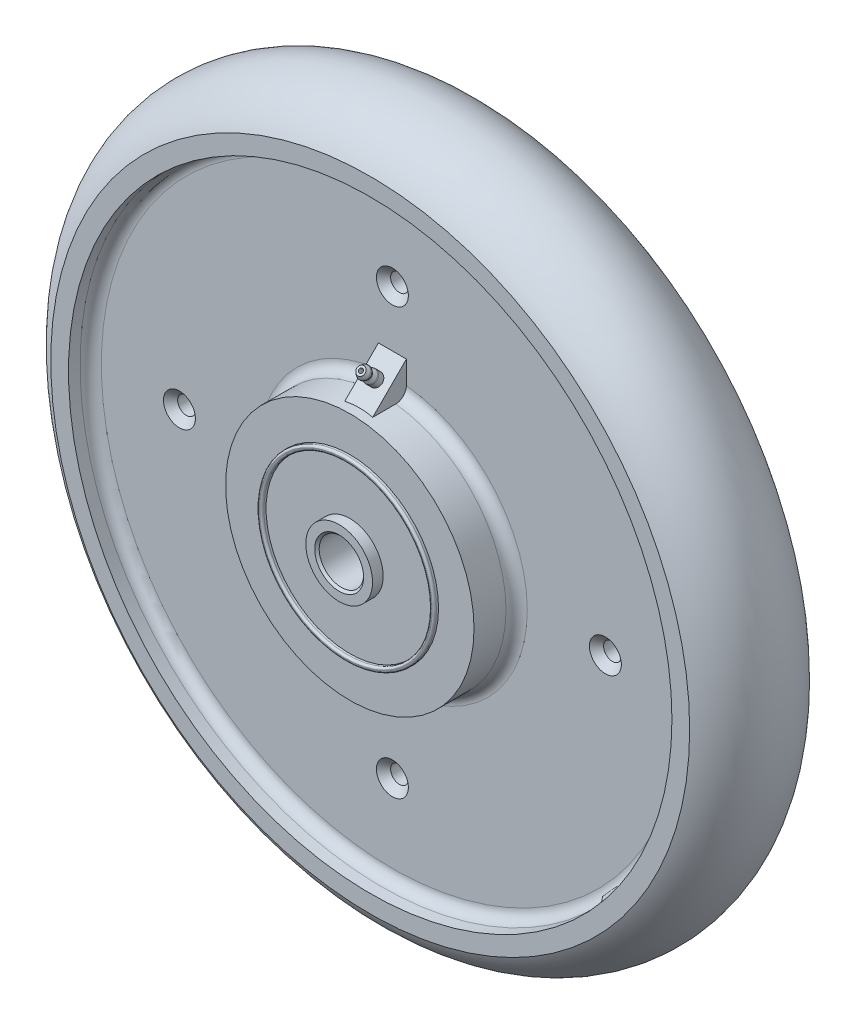
SolidWorks part; units mm, degrees
material "6061-T6 (SS)"
ref_plane "Front Plane" through (0, 0, 0) normal (0, 0, 1) x (1, 0, 0)
ref_plane "Top Plane" through (0, 0, 0) normal (0, 1, 0) x (1, 0, 0)
ref_plane "Right Plane" through (0, 0, 0) normal (1, 0, 0) x (0, 0, -1)
sketch "Sketch1" plane through (0, 0, 0) normal (1, 0, 0) x (0, 0, -1)
  line L0 (-31.75, 0) -> (31.75, 0) construction
  line L1 (31.75, -7.9375) -> (31.75, 7.9375) construction
  line L2 (0, -127) -> (0, 127) construction
  line L3 (-20.6375, 127) -> (20.6375, 127) construction
  line L4 (-20.6375, 127) -> (-20.6375, -127) construction
  line L5 (-20.6375, -127) -> (20.6375, -127) construction
  line L6 (20.6375, 127) -> (20.6375, -127) construction
  point P9 (-20.6375, 0)
  point P10 (0, 127)
  dimension "Hub Length" = 63.5
  dimension "For Axle Diameter" = 15.875
  dimension "Wheel Diameter" = 254
  dimension "Wheel Width" = 41.275
sketch "Sketch2" plane through (0, 0, 0) normal (1, 0, 0) x (0, 0, -1)
  line L0 (-31.75, 0) -> (31.75, 0) construction
  line L1 (-29.464, 31.75) -> (29.464, 31.75)
  line L2 (-29.464, 31.75) -> (-29.464, -31.75)
  line L3 (-29.464, -31.75) -> (29.464, -31.75)
  line L4 (29.464, 31.75) -> (29.464, -31.75)
  line L5 (-31.75, 11.9375) -> (31.75, 11.9375)
  line L6 (-31.75, 11.9375) -> (-31.75, -11.9375)
  line L7 (-31.75, -11.9375) -> (31.75, -11.9375)
  line L8 (31.75, 11.9375) -> (31.75, -11.9375)
  line L10 (-12.7, 107.95) -> (12.7, 107.95)
  line L11 (-12.7, 107.95) -> (-12.7, -107.95)
  line L12 (-12.7, -107.95) -> (12.7, -107.95)
  line L13 (12.7, 107.95) -> (12.7, -107.95)
  line L14 (-27.94, 44.45) -> (27.94, 44.45)
  line L15 (-27.94, 44.45) -> (-27.94, -44.45)
  line L16 (-27.94, -44.45) -> (27.94, -44.45)
  line L17 (27.94, 44.45) -> (27.94, -44.45)
  point P8 (-29.464, 0)
  point P11 (0, 31.75)
  point P19 (0, 107.95)
  point P20 (-12.7, 0)
  point P25 (-27.94, 0)
  point P26 (0, 44.45)
  dimension "Outer Hub Diameter" = 63.5
  dimension "Hub Diameter" = 23.875
  dimension "Outer Hub Length" = 58.928
  dimension "Inner Wheel Width" = 25.4
  dimension "Inner Wheel Diameter" = 215.9
  dimension "Wheel Hub Diameter" = 88.9
  dimension "Wheel Hub Length" = 55.88
sketch "Sketch3" plane through (0, 0, 0) normal (1, 0, 0) x (0, 0, -1)
  line L0 (0, -127) -> (0, 127) construction
  line L1 (-20.6375, 127) -> (-20.6375, 120.65) construction
  line L2 (-20.6375, 127) -> (-20.6375, -127) construction
  line L3 (-20.6375, 120.65) -> (-20.6375, 114.3) construction
  line L4 (-20.6375, 114.3) -> (-20.6375, 107.95) construction
  line L5 (0, -127) -> (0, 127) construction
  line L6 (27.94, 44.45) -> (27.94, -44.45) construction
  line L7 (-12.7, 107.95) -> (-12.7, -107.95) construction
  line L8 (-12.7, 107.95) -> (12.7, 107.95) construction
  line L9 (-20.6375, 114.3) -> (-20.6375, 107.95)
  line L10 (-20.6375, 107.95) -> (-12.7, 107.95) construction
  line L11 (-12.7, 107.95) -> (-12.7, 44.45) construction
  line L12 (-27.94, 44.45) -> (27.94, 44.45) construction
  line L13 (-12.7, 44.45) -> (-27.94, 44.45) construction
  line L14 (-27.94, 44.45) -> (-27.94, 31.75)
  line L15 (-29.464, 31.75) -> (29.464, 31.75) construction
  line L16 (-27.94, 44.45) -> (-27.94, -44.45) construction
  line L17 (-27.94, 31.75) -> (27.94, 31.75)
  line L19 (27.94, 31.75) -> (27.94, 44.45)
  line L20 (27.94, 44.45) -> (12.7, 44.45)
  line L21 (12.7, 107.95) -> (12.7, -107.95) construction
  line L22 (12.7, 44.45) -> (12.7, 107.95)
  line L23 (12.7, 107.95) -> (20.6375, 107.95)
  line L24 (20.6375, 127) -> (20.6375, -127) construction
  line L25 (20.6375, 107.95) -> (20.6375, 114.3)
  line L26 (-20.6375, 107.95) -> (-16.51, 107.95)
  line L27 (-12.7, 104.14) -> (-12.7, 48.26)
  line L28 (-16.51, 44.45) -> (-27.94, 44.45)
  line L29 (-27.94, 38.1) -> (-24.13, 38.1) construction
  line L30 (-24.13, 38.1) -> (-20.32, 38.1) construction
  line L31 (-20.32, 38.1) -> (-16.51, 38.1) construction
  line L32 (-16.51, 38.1) -> (-12.7, 38.1) construction
  line L33 (-16.51, 38.1) -> (-16.51, 48.26) construction
  arc A0 (20.6375, 114.3) -> (-20.6375, 114.3) centre (0, 103.882) ccw
  arc A1 (-16.51, 44.45) -> (-12.7, 48.26) centre (-16.51, 48.26) ccw
  arc A2 (-12.7, 104.14) -> (-16.51, 107.95) centre (-16.51, 104.14) ccw
revolve "Revolve1" add sketch "Sketch3" angle 360 about L0
sketch "Sketch4" plane through (0, 0, 0) normal (1, 0, 0) x (0, 0, -1)
  line L0 (31.75, 7.9375) -> (31.75, 11.9375)
  line L1 (31.75, 11.9375) -> (29.464, 11.9375)
  line L2 (29.464, 31.75) -> (29.464, -31.75) construction
  line L3 (-31.75, 11.9375) -> (31.75, 11.9375) construction
  line L4 (29.464, 11.9375) -> (29.464, 31.75)
  line L5 (29.464, 31.75) -> (-28.702, 31.75)
  line L6 (-29.464, 30.988) -> (-29.464, 30.734)
  line L8 (-27.94, 11.9375) -> (-31.75, 11.9375)
  line L9 (-31.75, 11.9375) -> (-31.75, 7.9375) construction
  line L10 (-31.75, 11.9375) -> (-31.75, -11.9375) construction
  line L11 (-30.95, 7.9375) -> (31.75, 7.9375)
  line L12 (-28.702, 29.972) -> (-27.94, 29.972)
  line L13 (-27.94, 29.972) -> (-27.94, 11.9375)
  line L14 (-30.95, 7.9375) -> (-31.75, 8.7375)
  line L15 (-31.75, 11.9375) -> (-31.75, 8.7375)
  line L16 (-30.95, 7.9375) -> (-30.95, 8.7375) construction
  line L17 (-30.95, 8.7375) -> (-30.95, 9.5375) construction
  line L18 (-30.95, 9.5375) -> (-30.95, 10.3375) construction
  line L19 (-30.95, 10.3375) -> (-30.95, 11.1375) construction
  line L20 (-30.95, 11.1375) -> (-30.95, 11.9375) construction
  line L21 (-30.95, 7.9375) -> (-31.75, 7.9375) construction
  arc A0 (-28.702, 31.75) -> (-29.464, 30.988) centre (-28.702, 30.988) ccw
  arc A1 (-29.464, 30.734) -> (-28.702, 29.972) centre (-28.702, 30.734) ccw
  point P16 (-29.464, 31.75)
  point P26 (-29.464, 29.972)
  dimension "D3" = 0.762
  dimension "D1" = 1.524
  dimension "D2" = 1.778
revolve "Revolve2" add sketch "Sketch4" angle 360 about L0
sketch "Sketch5" plane through (0, 0, 0) normal (1, 0, 0) x (0, 0, -1)
  line L0 (-24.4475, 44.45) -> (-12.7, 56.1975) construction
  line L1 (-18.5738, 50.3238) -> (-23.9619, 55.7119) construction
  line L2 (-23.9619, 55.7119) -> (-22.8928, 56.781) construction
  line L3 (-22.8928, 56.781) -> (-21.2052, 56.1881) construction
  line L4 (-21.2052, 56.1881) -> (-20.6215, 54.5268) construction
  line L5 (-20.6215, 54.5268) -> (-18.9602, 53.9431) construction
  line L6 (-18.9602, 53.9431) -> (-16.9573, 51.9402) construction
  line L7 (-21.2052, 56.1881) -> (-18.9602, 53.9431) construction
  line L8 (-16.9573, 51.9402) -> (-18.5738, 50.3238) construction
  line L9 (-23.4316, 56.2422) -> (-18.0434, 50.8541) construction
  line L10 (-23.4316, 56.2422) -> (-22.8928, 56.781) construction
  line L11 (-18.0434, 50.8541) -> (-16.9573, 51.9402) construction
  line L12 (-27.94, 44.45) -> (27.94, 44.45) construction
  line L13 (-12.7, 107.95) -> (-12.7, -107.95) construction
  line L14 (-25.3206, 43.5769) -> (-11.8269, 57.0706)
  line L15 (-11.8269, 57.0706) -> (-11.8269, 43.5769)
  line L16 (-11.8269, 43.5769) -> (-25.3206, 43.5769)
  line L17 (-27.94, 44.45) -> (-26.1938, 44.45) construction
  line L18 (-26.1938, 44.45) -> (-24.4475, 44.45) construction
  line L19 (-24.4475, 44.45) -> (-24.4475, 43.5769) construction
  line L20 (-12.7, 56.1975) -> (-11.8269, 56.1975) construction
  point P23 (-25.3206, 44.45)
  dimension "D1" = 7.62
  dimension "D2" = 0.762
  dimension "D3" = 3.175
  dimension "D4" = 45
  dimension "D5" = 2.286
  dimension "D6" = 0.762
  dimension "D7" = 0.75
  dimension "D8" = 3.4925
extrude "Boss-Extrude1" add sketch "Sketch5" along normal mid plane 10
sketch "Sketch6" plane through (0, 0, 0) normal (1, 0, 0) x (0, 0, -1)
  line L0 (-23.9619, 55.7119) -> (-22.8928, 56.781) construction
  line L1 (-22.8928, 56.781) -> (-21.2052, 56.1881) construction
  line L2 (-21.2052, 56.1881) -> (-20.6215, 54.5268) construction
  line L3 (-20.6215, 54.5268) -> (-18.9602, 53.9431) construction
  line L4 (-18.9602, 53.9431) -> (-16.9573, 51.9402) construction
  line L5 (-23.4316, 56.2422) -> (-18.0434, 50.8541) construction
  line L6 (-23.4316, 56.2422) -> (-22.8928, 56.781)
  line L7 (-22.8928, 56.781) -> (-21.6078, 56.3296)
  line L8 (-21.0638, 55.7855) -> (-20.6215, 54.5268)
  line L9 (-20.6215, 54.5268) -> (-19.1511, 54.0101)
  line L10 (-18.8171, 53.8) -> (-16.9573, 51.9402)
  line L11 (-23.4316, 56.2422) -> (-18.0434, 50.8541)
  line L12 (-25.3206, 43.5769) -> (-11.8269, 57.0706) construction
  line L13 (-18.0434, 50.8541) -> (-16.9573, 51.9402)
  line L14 (-18.5738, 50.3238) -> (-23.9619, 55.7119) construction
  line L15 (-18.5738, 50.3238) -> (-23.9619, 55.7119) construction
  arc A0 (-18.8171, 53.8) -> (-19.1511, 54.0101) centre (-19.4457, 53.1714) ccw
  arc A1 (-21.0638, 55.7855) -> (-21.6078, 56.3296) centre (-21.9025, 55.4909) ccw
  dimension "D1" = 0.889
revolve "Revolve3" add sketch "Sketch6" angle 360 about L15
sketch "Sketch7" plane through (0, 0, -27.94) normal (0, 0, -1) x (-1, 0, 0)
  circle A0 centre (0, 0) radius 76.2 construction
  circle A1 centre (0, 76.2) radius 3.175
  circle A2 centre (76.2, 0) radius 3.175
  circle A3 centre (0, -76.2) radius 3.175
  circle A4 centre (-76.2, 0) radius 3.175
  dimension "D1" = 152.4
  dimension "D2" = 6.35
extrude "Cut-Extrude1" cut sketch "Sketch7" against normal through all
chamfer "Chamfer1" distance 2.54 angle 45 8 edges at (-3.175, -76.2, 12.7) (3.175, -76.2, -12.7) (73.025, 0, 12.7) (79.375, 0, -12.7) (-79.375, 0, 12.7) (-73.025, 0, -12.7) (-3.175, 76.2, 12.7) (3.175, 76.2, -12.7)
